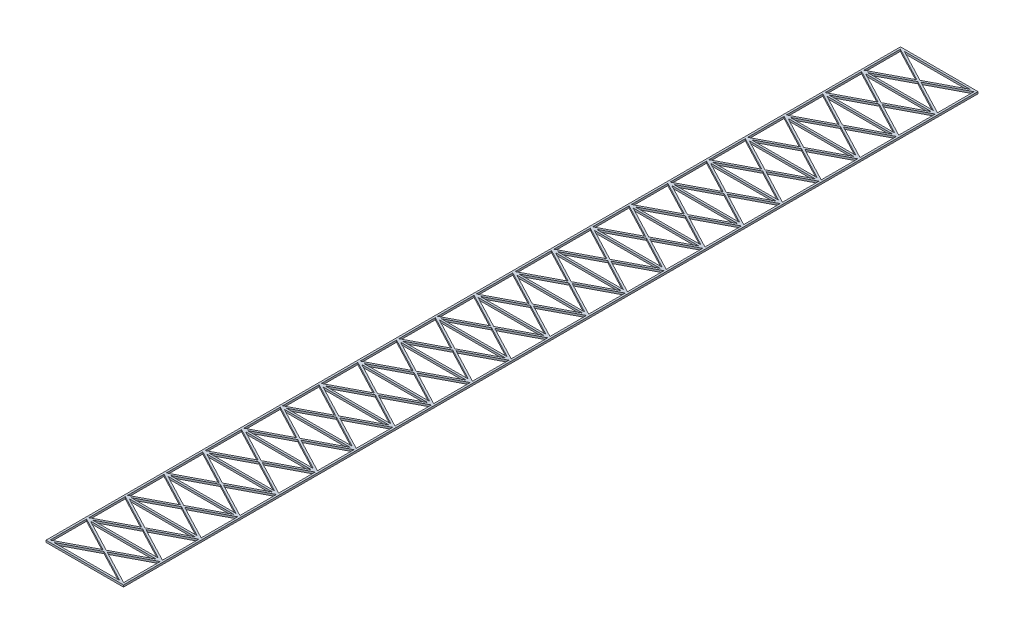
SolidWorks part; units mm, degrees
material "Polyester Resin"
ref_plane "Front Plane" through (0, 0, 0) normal (0, 0, 1) x (1, 0, 0)
ref_plane "Top Plane" through (0, 0, 0) normal (0, 1, 0) x (1, 0, 0)
ref_plane "Right Plane" through (0, 0, 0) normal (1, 0, 0) x (0, 0, -1)
sketch "Sketch1" plane through (0, 0, 0) normal (0, 1, 0) x (1, 0, 0)
  line L1 (-100, 0) -> (100, 0)
  line L2 (-100, 0) -> (-100, -105)
  line L3 (-100, -105) -> (100, -105)
  line L4 (100, 0) -> (100, -105)
  line L5 (-100, 0) -> (100, -105) construction
  line L6 (-100, -105) -> (100, 0) construction
  line L7 (-95, -5) -> (95, -5)
  line L8 (-95, -5) -> (-95, -100)
  line L9 (-95, -100) -> (95, -100)
  line L10 (95, -5) -> (95, -100)
  line L11 (-95, -5) -> (95, -100) construction
  line L12 (-95, -100) -> (95, -5) construction
  point P0 (0, -52.5)
  point P5 (0, -52.5)
  dimension "D1" = 200
  dimension "D2" = 105
  dimension "D3" = 5
  dimension "D4" = 5
extrude "Boss-Extrude1" add sketch "Sketch1" along normal blind 5
sketch "Sketch2" plane through (0, 0, 0) normal (0, -1, 0) x (1, 0, 0)
  line L0 (100, 0) -> (-100, 105) construction
  line L1 (100, 2.8236) -> (-94.6217, 105)
  line L2 (100, 105) -> (100, 0) construction
  line L3 (-100, 105) -> (100, 105) construction
  line L4 (94.6217, 0) -> (-100, 102.1764)
  line L5 (100, 0) -> (-100, 0) construction
  line L6 (-100, 0) -> (-100, 105) construction
  line L7 (94.6217, 0) -> (100, 2.8236)
  line L8 (-100, 102.1764) -> (-94.6217, 105)
  dimension "D1" = 2.5
  dimension "D2" = 2.5
extrude "Boss-Extrude2" add sketch "Sketch2" against normal up to surface (5 mm away) up to face at (0, 5, 52.5)
sketch "Sketch3" plane through (0, 0, 0) normal (0, -1, 0) x (1, 0, 0)
  line L0 (-100, 0) -> (100, 105) construction
  line L1 (100, 102.1764) -> (-94.6217, 0)
  line L2 (100, 105) -> (100, 0) construction
  line L3 (100, 0) -> (-100, 0) construction
  line L4 (-100, 2.8236) -> (94.6217, 105)
  line L5 (-100, 0) -> (-100, 105) construction
  line L6 (-100, 105) -> (100, 105) construction
  line L7 (-94.6217, 0) -> (-100, 2.8236)
  line L8 (100, 102.1764) -> (94.6217, 105)
  dimension "D1" = 2.5
  dimension "D2" = 2.5
extrude "Boss-Extrude3" add sketch "Sketch3" against normal up to surface (5 mm away) up to face at (34.9674, 5, 68.4829)
pattern_linear "LPattern1" count 22 spacing 100 along (0, 0, 1) of "Boss-Extrude1", "Boss-Extrude2", "Boss-Extrude3"
